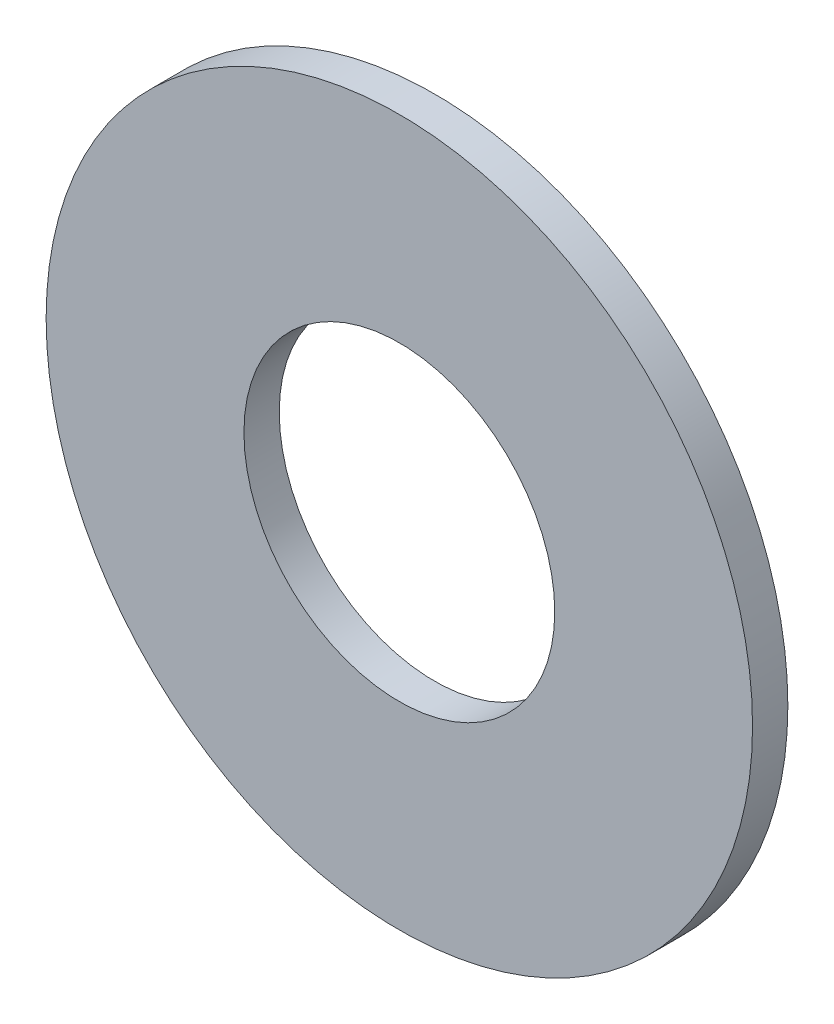
SolidWorks part; units mm, degrees
ref_plane "Front Plane" through (0, 0, 0) normal (0, 0, 1) x (1, 0, 0)
ref_plane "Top Plane" through (0, 0, 0) normal (0, 1, 0) x (1, 0, 0)
ref_plane "Right Plane" through (0, 0, 0) normal (1, 0, 0) x (0, 0, -1)
sketch "Sketch1" plane through (0, 0, 0) normal (0, 0, 1) x (1, 0, 0)
  circle A0 centre (0, 0) radius 1.1
  circle A1 centre (0, 0) radius 2.5
  dimension "ID" = 2.2
  dimension "OD" = 5
extrude "Extrude1" add sketch "Sketch1" against normal blind 0.25
